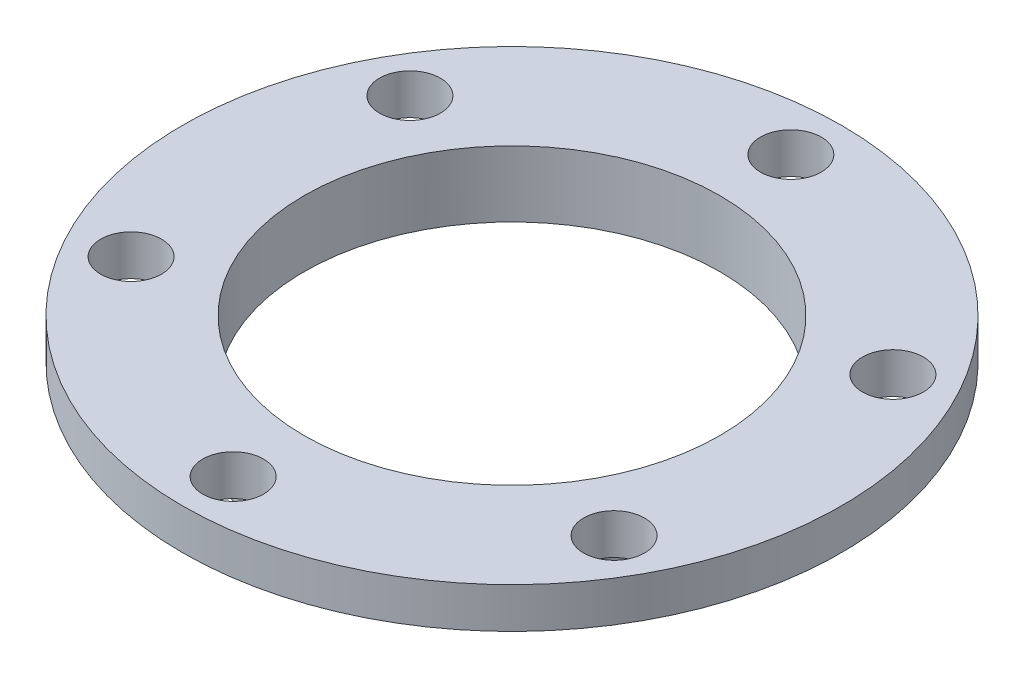
SolidWorks part; units mm, degrees
ref_plane "Front Plane" through (0, 0, 0) normal (0, 0, 1) x (1, 0, 0)
ref_plane "Top Plane" through (0, 0, 0) normal (0, 1, 0) x (1, 0, 0)
ref_plane "Right Plane" through (0, 0, 0) normal (1, 0, 0) x (0, 0, -1)
sketch "Sketch1" plane through (0, 0, 0) normal (0, 1, 0) x (1, 0, 0)
  circle A0 centre (0, 0) radius 32.5
  circle A1 centre (0, 0) radius 20.5
  dimension "D1" = 65
  dimension "D2" = 41
extrude "Boss-Extrude1" add sketch "Sketch1" along normal blind 4
sketch "Sketch2" plane through (0, 0, 0) normal (0, -1, 0) x (1, 0, 0)
  circle A0 centre (0, 0) radius 20.5
  circle A1 centre (0, 0) radius 23.5
  dimension "D1" = 47
extrude "Boss-Extrude2" add sketch "Sketch2" along normal blind 2.5
sketch "Sketch3" plane through (0, 4, 0) normal (0, 1, 0) x (1, 0, 0)
  circle A0 centre (0, 0) radius 27.5 construction
  circle A1 centre (0, 27.5) radius 3
  circle A5 centre (23.8157, 13.75) radius 3
  circle A6 centre (23.8157, -13.75) radius 3
  circle A7 centre (0, -27.5) radius 3
  circle A8 centre (-23.8157, -13.75) radius 3
  circle A9 centre (-23.8157, 13.75) radius 3
  dimension "D1" = 55
  dimension "D3" = 6
  dimension "D2" = 6
extrude "Cut-Extrude1" cut sketch "Sketch3" against normal through all both and the other way through all
